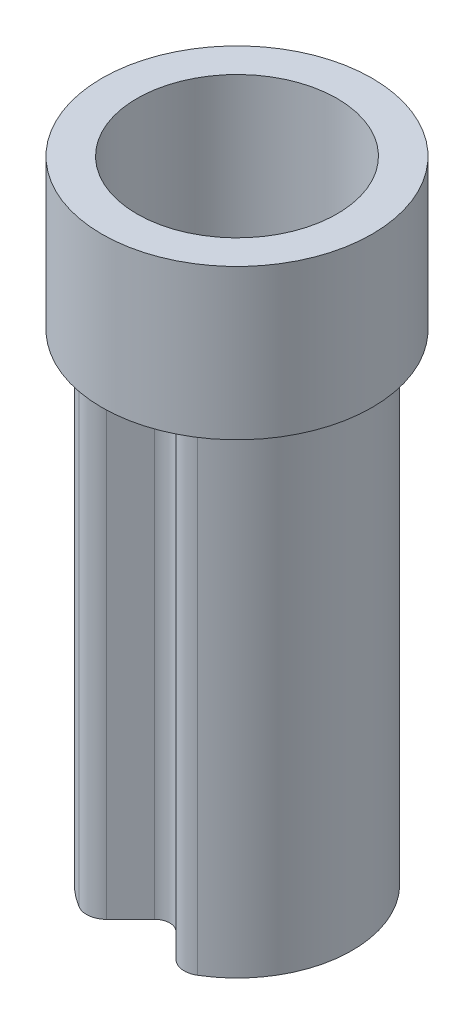
SolidWorks part; units mm, degrees
ref_plane "Front Plane" through (0, 0, 0) normal (0, 0, 1) x (1, 0, 0)
ref_plane "Top Plane" through (0, 0, 0) normal (0, 1, 0) x (1, 0, 0)
ref_plane "Right Plane" through (0, 0, 0) normal (1, 0, 0) x (0, 0, -1)
sketch "Sketch1" plane through (0, 0, 0) normal (0, 1, 0) x (1, 0, 0)
  line L0 (0, 0) -> (0, -1.15) construction
  line L1 (-0.4488, -1.0588) -> (-0.1061, -0.7161)
  line L2 (0.1061, -0.7161) -> (0.4488, -1.0588)
  line L3 (-0.4796, -0.8775) -> (-0.2121, -0.61)
  line L4 (0.2121, -0.61) -> (0.4796, -0.8775)
  arc A0 (0.4488, -1.0588) -> (-0.4488, -1.0588) centre (0, 0) ccw
  arc A1 (0.1061, -0.7161) -> (-0.1061, -0.7161) centre (0, -0.8221) ccw
  arc A2 (0.2121, -0.61) -> (-0.2121, -0.61) centre (0, -0.8221) ccw
  arc A3 (0.4796, -0.8775) -> (-0.4796, -0.8775) centre (0, 0) ccw
  point P8 (0, -0.61)
  dimension "D1" = 2.3
  dimension "D3" = 0.15
  dimension "D2" = 0.61
  dimension "D4" = 0.15
extrude "Boss-Extrude1" add sketch "Sketch1" along normal blind 4.8 contours A3 L3 A2 L4
fillet "Fillet1" radius 0.05 2 edges at (0.4796, 2.4, 0.8775) (-0.4796, 2.4, 0.8775)
fillet "Fillet2" radius 0.2 2 edges at (0.4488, 2.4, 1.0588) (-0.4488, 2.4, 1.0588)
sketch "Sketch2" plane through (0, 4.8, 0) normal (0, 1, 0) x (1, 0, 0)
  circle A0 centre (0, 0) radius 1.35
  circle A1 centre (0, 0) radius 1
  arc A2 (0.5136, -0.858) -> (-0.5136, -0.858) centre (0, 0) ccw construction
  dimension "D1" = 2.7
extrude "Boss-Extrude2" add sketch "Sketch2" along normal offset from surface (1.5 mm away) 6.3 up to face at (0, 0, 0.537)
